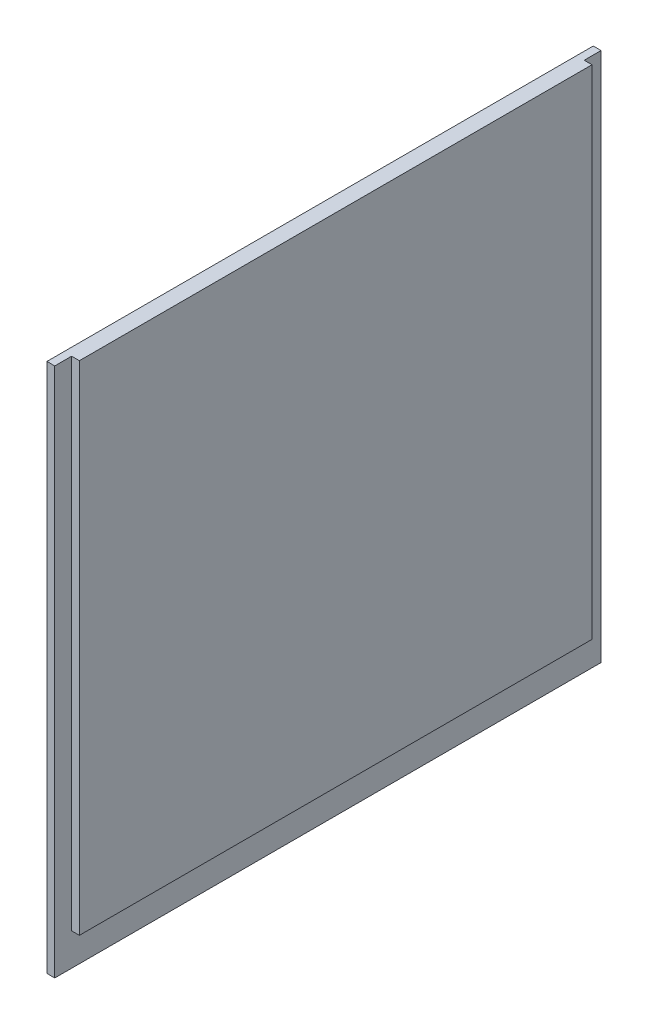
SolidWorks part; units mm, degrees
ref_plane "Front Plane" through (0, 0, 0) normal (0, 0, 1) x (1, 0, 0)
ref_plane "Top Plane" through (0, 0, 0) normal (0, 1, 0) x (1, 0, 0)
ref_plane "Right Plane" through (0, 0, 0) normal (1, 0, 0) x (0, 0, -1)
sketch "Sketch1" plane through (0, 0, 0) normal (1, 0, 0) x (0, 0, -1)
  line L1 (0, 0) -> (111.252, 0)
  line L2 (0, 0) -> (0, 107.95)
  line L3 (0, 107.95) -> (111.252, 107.95)
  line L4 (111.252, 0) -> (111.252, 107.95)
  dimension "D1" = 111.252
  dimension "D2" = 107.95
extrude "Boss-Extrude1" add sketch "Sketch1" along normal blind 1.5875
sketch "Sketch2" plane through (1.5875, 0, 0) normal (1, 0, 0) x (0, 0, -1)
  line L0 (111.252, 107.95) -> (0, 107.95) construction
  line L1 (3.429, 107.95) -> (107.823, 107.95)
  line L2 (3.429, 107.95) -> (3.429, 6.604)
  line L3 (3.429, 6.604) -> (107.823, 6.604)
  line L4 (107.823, 107.95) -> (107.823, 6.604)
  line L5 (0, 0) -> (111.252, 0) construction
  line L6 (0, 107.95) -> (0, 0) construction
  line L7 (111.252, 0) -> (111.252, 107.95) construction
  dimension "D1" = 6.604
  dimension "D2" = 3.429
  dimension "D3" = 3.429
extrude "Boss-Extrude2" add sketch "Sketch2" along normal blind 1.5875
